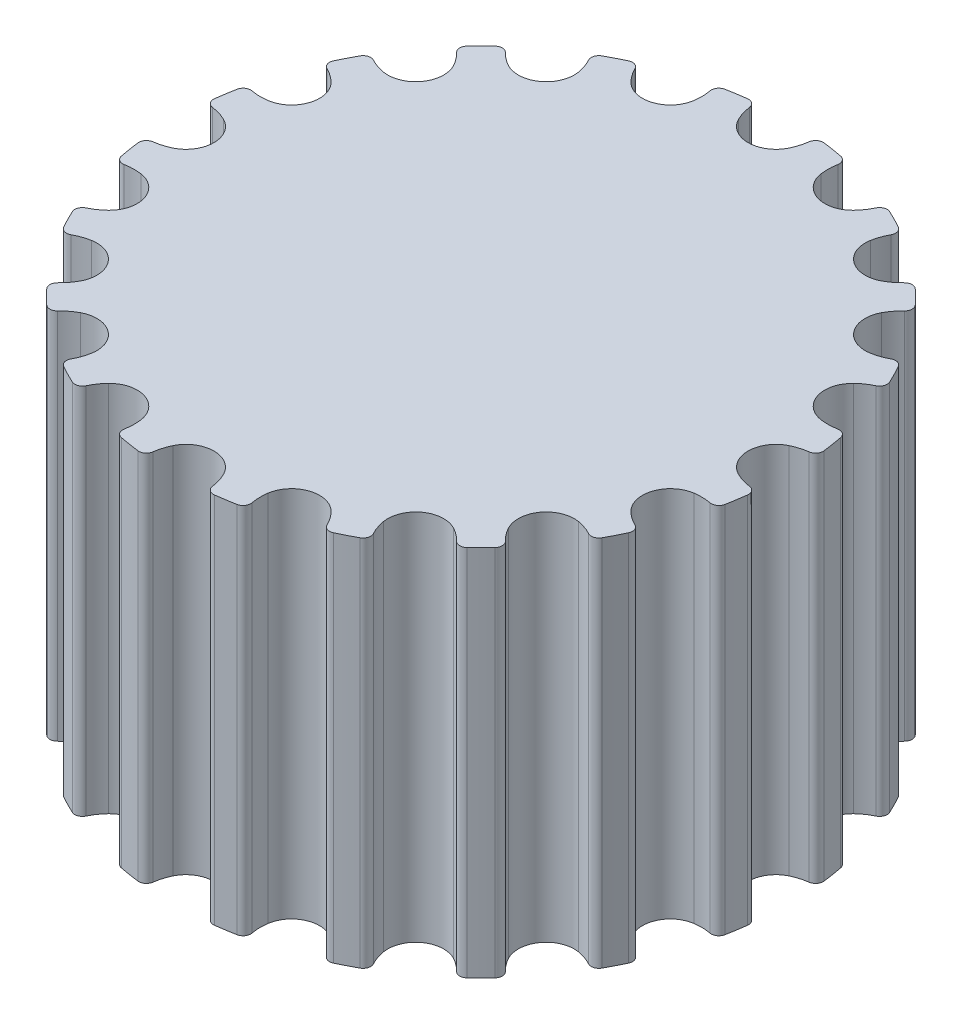
SolidWorks part; units mm, degrees
other "DetailItem1"
other "DetailItem2"
ref_plane "Front Plane" through (0, 0, 0) normal (0, 0, 1) x (1, 0, 0)
ref_plane "Top Plane" through (0, 0, 0) normal (0, 1, 0) x (1, 0, 0)
ref_plane "Right Plane" through (0, 0, 0) normal (1, 0, 0) x (0, 0, -1)
sketch "Sketch1" plane through (0, 0, 0) normal (0, 1, 0) x (1, 0, 0)
  circle A0 centre (0, 0) radius 3
  circle A2 centre (0, 0) radius 6.1
  dimension "D1" = 6
  dimension "D3" = 12.2
extrude "Boss-Extrude1" add sketch "Sketch1" along normal blind 7.4
sketch "Sketch2" plane through (0, 7.4, 0) normal (0, 1, 0) x (1, 0, 0)
  line L0 (0, 6.1) -> (0, 0) construction
  line L1 (10.4749, 4.4585) -> (22.879, 4.4585) construction
  arc A0 (-0.4989, 5.6144) -> (0.4989, 5.6144) centre (0, 5.8576) ccw
  circle A1 centre (0, 0) radius 6.1
  circle A2 centre (0, 0) radius 6.1
  arc A3 (-0.4989, 5.6144) -> (-0.5916, 5.9232) centre (0.4, 6.0526) cw
  arc A4 (-0.5916, 5.9232) -> (-0.759, 6.0526) centre (-0.7403, 5.9038) ccw
  arc A5 (0.5916, 5.9232) -> (0.759, 6.0526) centre (0.7403, 5.9038) cw
  arc A6 (0.4989, 5.6144) -> (0.5916, 5.9232) centre (-0.4, 6.0526) ccw
  point P12 (0, 5.3026)
  dimension "D2" = 0.555
  dimension "D3" = 0.15
  dimension "D4" = 1
  dimension "D5" = 0.4
  dimension "D6" = 0.75
  dimension "D1" = 0
extrude "Cut-Extrude2" cut sketch "Sketch2" against normal up to surface (7.4 mm away) contours A0 A6 A5 A2 A4 A3
pattern_circular "CirPattern1" count 20 over 360 about axis through (0, 0, 0) along (0, 1, 0) of "Cut-Extrude2"
